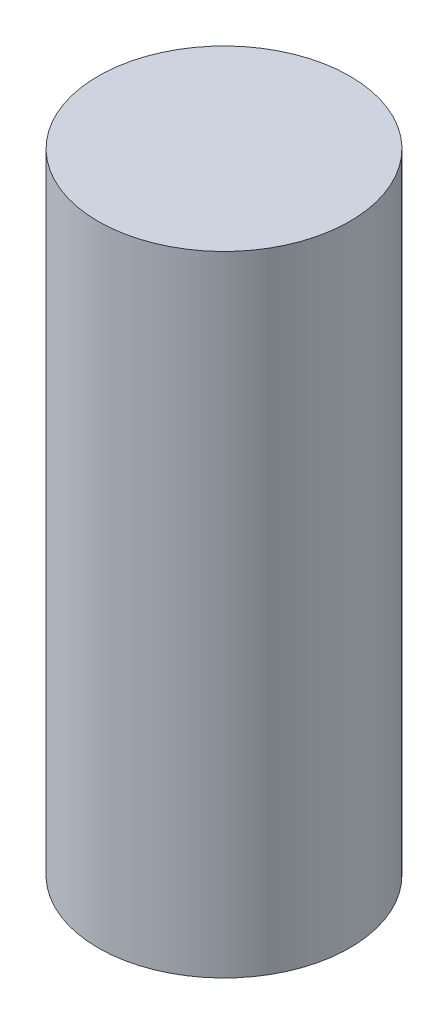
SolidWorks part; units mm, degrees
ref_plane "Front Plane" through (0, 0, 0) normal (0, 0, 1) x (1, 0, 0)
ref_plane "Top Plane" through (0, 0, 0) normal (0, 1, 0) x (1, 0, 0)
ref_plane "Right Plane" through (0, 0, 0) normal (1, 0, 0) x (0, 0, -1)
sketch "스케치1" plane through (0, 0, 0) normal (0, 1, 0) x (1, 0, 0)
  circle A0 centre (0, 0) radius 13
extrude "보스-돌출1" add sketch "스케치1" along normal blind 65
